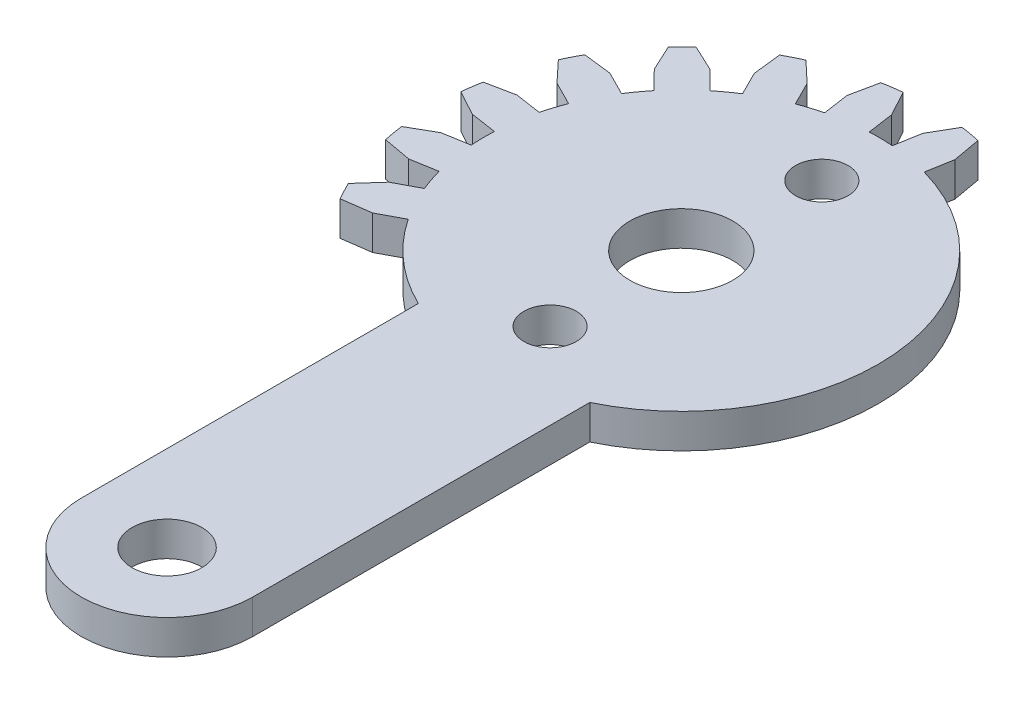
SolidWorks part; units mm, degrees
ref_plane "Alzado" through (0, 0, 0) normal (0, 0, 1) x (1, 0, 0)
ref_plane "Planta" through (0, 0, 0) normal (0, 1, 0) x (1, 0, 0)
ref_plane "Vista lateral" through (0, 0, 0) normal (1, 0, 0) x (0, 0, -1)
sketch "Croquis1" plane through (0, 0, 0) normal (0, 1, 0) x (1, 0, 0)
  line L0 (0, 0) -> (0, -30) construction
  line L1 (-5, -10.3395) -> (-5, -30)
  line L2 (5, -10.3395) -> (5, -30)
  line L5 (0, 0) -> (12.7, 0) construction
  arc A0 (5, -10.3395) -> (-5, -10.3395) centre (0, 0) ccw
  arc A1 (-5, -30) -> (5, -30) centre (0, -30) ccw
  circle A2 centre (0, -30) radius 2.0343
  circle A3 centre (0, 0) radius 3
  circle A4 centre (0, 0) radius 11.485 construction
  point P9 (0, 11.485)
  point P10 (0, -35)
  dimension "D1" = 22.97
  dimension "D3" = 30
  dimension "D2" = 10
  dimension "D4" = 6
extrude "Saliente-Extruir1" add sketch "Croquis1" along normal blind 2
sketch "Croquis3" plane through (0, 0, 0) normal (0, 1, 0) x (1, 0, 0)
  line L0 (2.5261, 14.3265) -> (1.9943, 11.3105) construction
  line L1 (1.9943, 11.3105) -> (0, 0) construction
  line L2 (1.1204, 12.9679) -> (0.8534, 11.4533)
  line L3 (3.3824, 12.5691) -> (3.1153, 11.0544)
  line L4 (1.9587, 14.415) -> (1.1204, 12.9679)
  line L5 (3.0897, 14.2156) -> (3.3824, 12.5691)
  line L6 (0, 0) -> (11.485, 0) construction
  circle A0 centre (0, 0) radius 14.5475 construction
  circle A1 centre (0, 0) radius 11.485 construction
  circle A2 centre (0, 0) radius 13.0162 construction
  arc A3 (5, -10.3395) -> (-5, -10.3395) centre (0, 0) ccw construction
  arc A4 (3.0897, 14.2156) -> (1.9587, 14.415) centre (0, 0) ccw
  arc A5 (3.1153, 11.0544) -> (0.8534, 11.4533) centre (0, 0) ccw
  point P9 (2.2602, 12.8185)
  dimension "D1" = 3.0625
  dimension "D4" = 80
  dimension "D2" = 1.1484
  dimension "D3" = 2.2969
extrude "Saliente-Extruir2" add sketch "Croquis3" along normal up to surface (2 mm away) up to face at (0, 2, 32.0343)
pattern_circular "MatrizC1" count 8 over 128 about axis through (0, 0, 0) along (0, 1, 0) of "Saliente-Extruir2"
sketch "Croquis4" plane through (0, 0, 0) normal (0, -1, 0) x (1, 0, 0)
  line L0 (0, 0) -> (0.6418, -8.7504) construction
  circle A0 centre (0.56, -7.6345) radius 1.53
  circle A1 centre (0, 0) radius 7.655 construction
  circle A2 centre (0, 7.655) radius 1.53
  dimension "D1" = 3.06
  dimension "D2" = 15.31
extrude "Cortar-Extruir1" cut sketch "Croquis4" against normal blind 10
